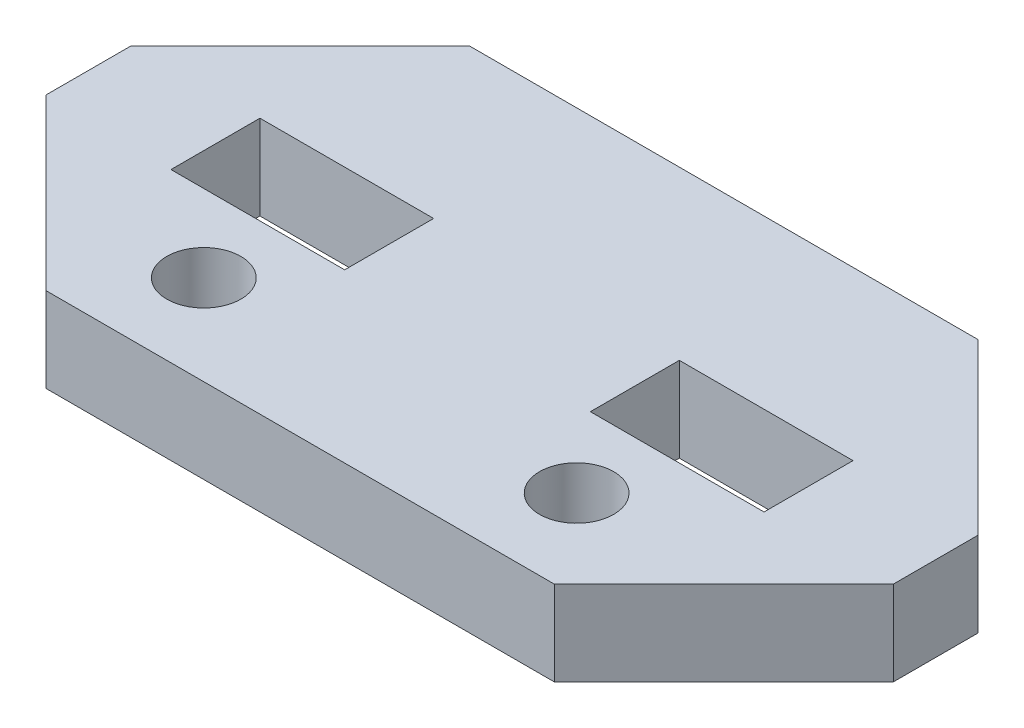
SolidWorks part; units mm, degrees
ref_plane "Front Plane" through (0, 0, 0) normal (0, 0, 1) x (1, 0, 0)
ref_plane "Top Plane" through (0, 0, 0) normal (0, 1, 0) x (1, 0, 0)
ref_plane "Right Plane" through (0, 0, 0) normal (1, 0, 0) x (0, 0, -1)
sketch "Sketch1" plane through (0, 0, 0) normal (0, 1, 0) x (1, 0, 0)
  line L1 (12, -10) -> (-12, -10)
  line L2 (20, -2) -> (20, 2)
  line L3 (12, 10) -> (-12, 10)
  line L4 (-20, -2) -> (-20, 2)
  line L14 (-12, -10) -> (-20, -2)
  line L15 (-20, 2) -> (-12, 10)
  line L16 (12, 10) -> (20, 2)
  line L17 (20, -2) -> (12, -10)
  point P0 (0, 0)
  point P16 (9.9, 0)
extrude "Boss-Extrude1" add sketch "Sketch1" along normal blind 4 contours L1 L14 L4 L15 L3 L16 L2 L17
sketch "Sketch2" plane through (0, 4, 0) normal (0, 1, 0) x (1, 0, 0)
  line L0 (-20, 0) -> (20, 0) construction
  line L1 (-20, -2) -> (-20, 2) construction
  line L2 (20, -2) -> (20, 2) construction
  line L3 (0, 10) -> (0, -10) construction
  line L4 (12, 10) -> (-12, 10) construction
  line L5 (12, -10) -> (-12, -10) construction
  line L6 (-5.8, 2.1) -> (-14, -2.1) construction
  line L7 (5.8, -2.1) -> (14, -2.1)
  line L8 (5.8, -2.1) -> (5.8, 2.1)
  line L9 (5.8, 2.1) -> (14, 2.1)
  line L10 (14, -2.1) -> (14, 2.1)
  line L11 (5.8, -2.1) -> (14, 2.1) construction
  line L12 (5.8, 2.1) -> (14, -2.1) construction
  line L13 (-5.8, -2.1) -> (-14, 2.1) construction
  line L14 (-14, -2.1) -> (-14, 2.1)
  line L15 (-5.8, 2.1) -> (-14, 2.1)
  line L16 (-5.8, -2.1) -> (-5.8, 2.1)
  line L17 (-5.8, -2.1) -> (-14, -2.1)
  point P12 (9.9, 0)
  point P21 (-9.9, 0)
  dimension "D1" = 8.2
  dimension "D2" = 4.2
  dimension "D3" = 6
extrude "Cut-Extrude1" cut sketch "Sketch2" against normal up to surface (4 mm away) contours L14 L15 L16 L17 | L8 L7 L10 L9 up to face at (0, 0, 0)
sketch "Sketch3" plane through (0, 4, 0) normal (0, 1, 0) x (1, 0, 0)
  line L0 (-8.8, -7.5) -> (-8.8, -10) construction
  line L1 (12, -10) -> (-12, -10) construction
  line L2 (-10.55, -5.75) -> (-16.25, -5.75) construction
  line L4 (-12, -10) -> (-20, -2) construction
  line L7 (-16.25, -5.75) -> (-7.05, -5.75) construction
  line L8 (20, -2) -> (12, -10) construction
  line L9 (10.55, -5.75) -> (16.25, -5.75) construction
  line L10 (7.05, -5.75) -> (16.25, -5.75) construction
  circle A0 centre (-8.8, -5.75) radius 1.75
  circle A1 centre (8.8, -5.75) radius 1.75
  dimension "D1" = 2.5
  dimension "D2" = 14.1
  dimension "D3" = 3.5
extrude "Cut-Extrude2" cut sketch "Sketch3" against normal up to surface (4 mm away) up to face at (-9.9, 0, 0)
